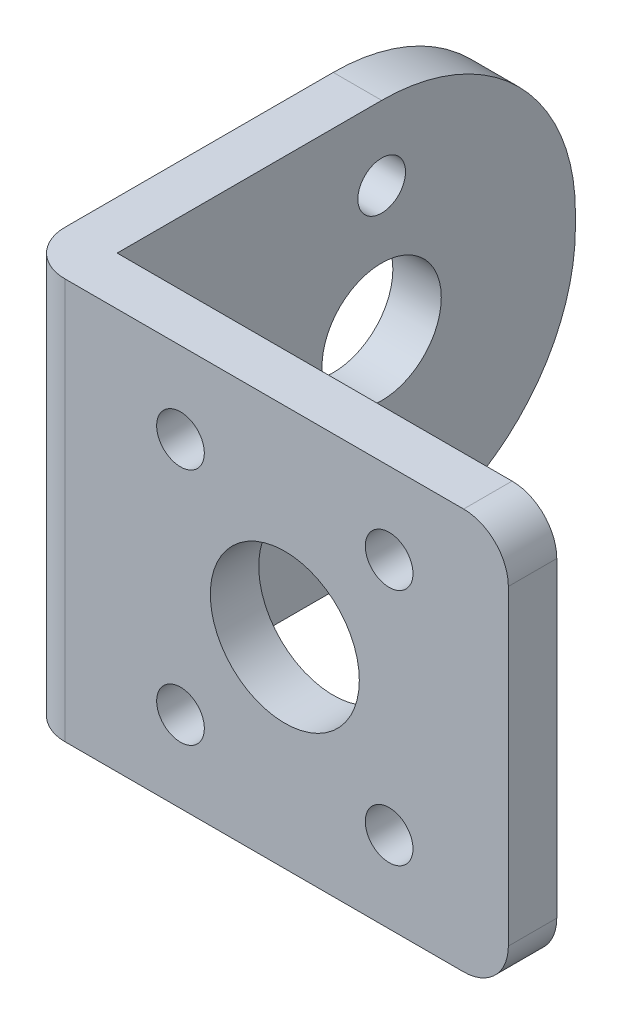
SolidWorks part; units mm, degrees
ref_plane "Front Plane" through (0, 0, 0) normal (0, 0, 1) x (1, 0, 0)
ref_plane "Top Plane" through (0, 0, 0) normal (0, 1, 0) x (1, 0, 0)
ref_plane "Right Plane" through (0, 0, 0) normal (1, 0, 0) x (0, 0, -1)
sketch "Sketch1" plane through (0, 0, 0) normal (0, 0, 1) x (1, 0, 0)
  line L1 (0, 0) -> (32.75, 0)
  line L2 (0, 0) -> (0, 26.9)
  line L3 (0, 26.9) -> (32.75, 26.9)
  line L4 (32.75, 0) -> (32.75, 26.9)
  dimension "D1" = 26.9
  dimension "D2" = 32.75
extrude "Boss-Extrude1" add sketch "Sketch1" along normal blind 3.25
fillet "Fillet1" radius 3 2 edges at (32.75, 0, 1.625) (32.75, 26.9, 1.625)
sketch "Sketch2" plane through (0, 0, 3.25) normal (0, 0, 1) x (1, 0, 0)
  line L0 (0, 26.9) -> (0, 0) construction
  line L1 (32.75, 3) -> (32.75, 23.9) construction
  line L2 (10.75, 5.45) -> (24.75, 5.45)
  line L3 (10.75, 5.45) -> (10.75, 21.45)
  line L4 (10.75, 21.45) -> (24.75, 21.45)
  line L5 (24.75, 5.45) -> (24.75, 21.45)
  line L6 (10.75, 5.45) -> (24.75, 21.45) construction
  line L7 (10.75, 21.45) -> (24.75, 5.45) construction
  circle A0 centre (17.75, 13.45) radius 5
  circle A1 centre (10.75, 21.45) radius 1.6
  circle A2 centre (24.75, 21.45) radius 1.6
  circle A3 centre (24.75, 5.45) radius 1.6
  circle A4 centre (10.75, 5.45) radius 1.6
  point P5 (0, 13.45)
  dimension "D1" = 10
  dimension "D4" = 3.2
  dimension "D5" = 15
  dimension "D2" = 16
  dimension "D3" = 14
extrude "Cut-Extrude1" cut sketch "Sketch2" against normal blind 3.25 contours L4 A1 L3 | L3 A1 L4 | A0 | A2 | A3 | A4
sketch "Sketch4" plane through (0, 0, 0) normal (0, 0, -1) x (-1, 0, 0)
  line L0 (-29.75, 26.9) -> (0, 26.9) construction
  line L1 (0, 0) -> (-3.25, 0)
  line L2 (0, 0) -> (0, 26.9)
  line L3 (0, 26.9) -> (-3.25, 26.9)
  line L4 (-3.25, 0) -> (-3.25, 26.9)
  dimension "D1" = 3.25
extrude "Boss-Extrude2" add sketch "Sketch4" along normal blind 30.75
fillet "Fillet2" radius 3 1 edges at (0, 13.45, 3.25)
sketch "Sketch5" plane through (3.25, 0, 0) normal (1, 0, 0) x (0, 0, -1)
  line L0 (30.75, 26.9) -> (30.75, 0) construction
  line L1 (10.982, 4.95) -> (24.518, 4.95)
  line L2 (10.982, 4.95) -> (10.982, 21.95)
  line L3 (10.982, 21.95) -> (24.518, 21.95)
  line L4 (24.518, 4.95) -> (24.518, 21.95)
  line L5 (10.982, 4.95) -> (24.518, 21.95) construction
  line L6 (10.982, 21.95) -> (24.518, 4.95) construction
  circle A0 centre (17.75, 13.45) radius 4
  circle A1 centre (17.75, 21.95) radius 1.6
  circle A2 centre (17.75, 4.95) radius 1.6
  point P9 (30.75, 13.45)
  dimension "D1" = 8
  dimension "D3" = 13
  dimension "D4" = 3.2
  dimension "D2" = 17
extrude "Cut-Extrude2" cut sketch "Sketch5" against normal blind 30.75 contours A1 | A0 | A2
fillet "Fillet4" radius 13 2 edges at (1.625, 0, -30.75) (1.625, 26.9, -30.75)
